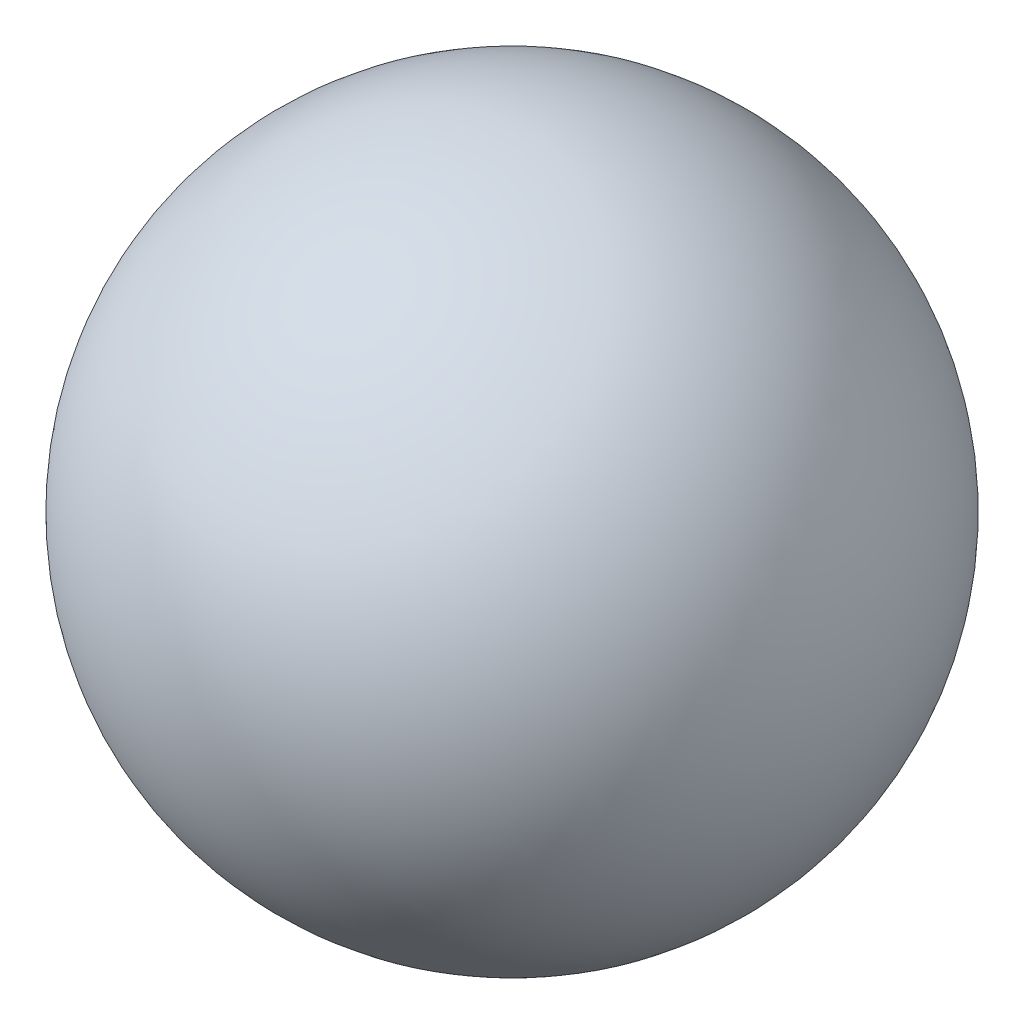
SolidWorks part; units mm, degrees
ref_plane "Front Plane" through (0, 0, 0) normal (0, 0, 1) x (1, 0, 0)
ref_plane "Top Plane" through (0, 0, 0) normal (0, 1, 0) x (1, 0, 0)
ref_plane "Right Plane" through (0, 0, 0) normal (1, 0, 0) x (0, 0, -1)
sketch "Sketch1" plane through (0, 0, 0) normal (0, 0, 1) x (1, 0, 0)
  line L0 (0, 1620) -> (0, -1620)
  arc A0 (0, -1620) -> (0, 1620) centre (0, 0) ccw
  dimension "D1" = 3240
revolve "Revolve1" add sketch "Sketch1" angle 360 about L0
